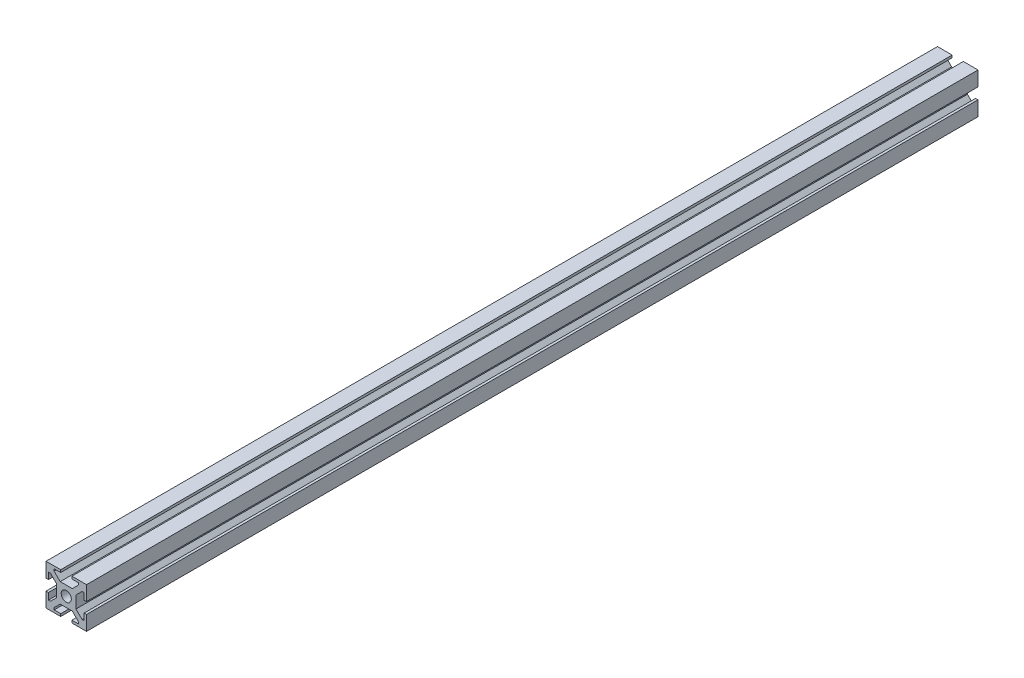
SolidWorks part; units mm, degrees
ref_plane "Plan de face" through (0, 0, 0) normal (0, 0, 1) x (1, 0, 0)
ref_plane "Plan de dessus" through (0, 0, 0) normal (0, 1, 0) x (1, 0, 0)
ref_plane "Plan de droite" through (0, 0, 0) normal (1, 0, 0) x (0, 0, -1)
sketch "Esquisse1" plane through (0, 0, 0) normal (0, 0, 1) x (1, 0, 0)
  line L1 (-22.5051, 0.0904) -> (-2.5051, 0.0904)
  line L2 (-22.5051, 0.0904) -> (-22.5051, -19.9096)
  line L3 (-22.5051, -19.9096) -> (-2.5051, -19.9096)
  line L4 (-2.5051, 0.0904) -> (-2.5051, -19.9096)
  dimension "D1" = 20
  dimension "D2" = 20
extrude "Boss.-Extru.1" add sketch "Esquisse1" along normal blind 440
sketch "Esquisse2" plane through (0, 0, 440) normal (0, 0, 1) x (1, 0, 0)
  line L0 (-22.5051, 0.0904) -> (-22.5051, -19.9096) construction
  line L1 (-22.5051, -7.1596) -> (-21.3051, -7.1596)
  line L2 (-22.5051, -7.1596) -> (-22.5051, -12.6596)
  line L3 (-22.5051, -12.6596) -> (-21.3051, -12.6596)
  line L4 (-21.3051, -7.1596) -> (-21.3051, -12.6596)
  line L5 (-2.5051, 0.0904) -> (-22.5051, 0.0904) construction
  line L6 (-15.2551, 0.0904) -> (-9.7551, 0.0904)
  line L7 (-15.2551, 0.0904) -> (-15.2551, -1.1096)
  line L8 (-15.2551, -1.1096) -> (-9.7551, -1.1096)
  line L9 (-9.7551, 0.0904) -> (-9.7551, -1.1096)
  line L10 (-2.5051, -19.9096) -> (-2.5051, 0.0904) construction
  line L11 (-2.5051, -7.1596) -> (-3.7051, -7.1596)
  line L12 (-2.5051, -7.1596) -> (-2.5051, -12.6596)
  line L13 (-2.5051, -12.6596) -> (-3.7051, -12.6596)
  line L14 (-3.7051, -7.1596) -> (-3.7051, -12.6596)
  line L15 (-22.5051, -19.9096) -> (-2.5051, -19.9096) construction
  line L16 (-15.2551, -19.9096) -> (-9.7551, -19.9096)
  line L17 (-15.2551, -19.9096) -> (-15.2551, -18.7096)
  line L18 (-15.2551, -18.7096) -> (-9.7551, -18.7096)
  line L19 (-9.7551, -19.9096) -> (-9.7551, -18.7096)
  dimension "D1" = 1.2
  dimension "D2" = 1.2
  dimension "D3" = 1.2
  dimension "D4" = 1.2
  dimension "D5" = 5.5
  dimension "D6" = 5.5
  dimension "D7" = 5.5
  dimension "D8" = 5.5
  dimension "D9" = 7.25
  dimension "D10" = 7.25
  dimension "D11" = 7.25
  dimension "D12" = 7.25
extrude "Enlèv. mat.-Extru.1" cut sketch "Esquisse2" against normal through all
sketch "Esquisse3" plane through (0, 0, 440) normal (0, 0, 1) x (1, 0, 0)
  line L0 (-15.2551, 0.0904) -> (-22.5051, 0.0904) construction
  line L1 (-21.3051, -15.9096) -> (-20.3051, -15.9096)
  line L2 (-21.3051, -15.9096) -> (-21.3051, -3.9096)
  line L3 (-21.3051, -3.9096) -> (-20.3051, -3.9096)
  line L4 (-17.3051, -12.9096) -> (-17.3051, -6.9096)
  line L5 (-18.5051, -1.1096) -> (-6.5051, -1.1096)
  line L6 (-18.5051, -1.1096) -> (-18.5051, -2.1096)
  line L7 (-15.5051, -5.1096) -> (-9.5051, -5.1096)
  line L8 (-6.5051, -1.1096) -> (-6.5051, -2.1096)
  line L9 (-3.7051, -3.9096) -> (-4.7051, -3.9096)
  line L10 (-3.7051, -3.9096) -> (-3.7051, -15.9096)
  line L11 (-3.7051, -15.9096) -> (-4.7051, -15.9096)
  line L12 (-7.7051, -6.9096) -> (-7.7051, -12.9096)
  line L13 (-6.5051, -18.7096) -> (-18.5051, -18.7096)
  line L14 (-6.5051, -18.7096) -> (-6.5051, -17.7096)
  line L15 (-9.5051, -14.7096) -> (-15.5051, -14.7096)
  line L16 (-18.5051, -18.7096) -> (-18.5051, -17.7096)
  line L17 (-2.5051, -7.1596) -> (-2.5051, 0.0904) construction
  line L18 (-15.2551, -1.1096) -> (-9.7551, -1.1096) construction
  line L19 (-3.7051, -7.1596) -> (-3.7051, -12.6596) construction
  line L20 (-9.7551, -19.9096) -> (-2.5051, -19.9096) construction
  line L21 (-22.5051, -12.6596) -> (-22.5051, -19.9096) construction
  line L22 (-22.5051, -19.9096) -> (-15.2551, -19.9096) construction
  line L23 (-15.5051, -14.7096) -> (-18.5051, -17.7096)
  line L24 (-20.3051, -15.9096) -> (-17.3051, -12.9096)
  line L25 (-6.5051, -17.7096) -> (-9.5051, -14.7096)
  line L26 (-4.7051, -15.9096) -> (-7.7051, -12.9096)
  line L27 (-4.7051, -3.9096) -> (-7.7051, -6.9096)
  line L28 (-9.5051, -5.1096) -> (-6.5051, -2.1096)
  line L29 (-18.5051, -2.1096) -> (-15.5051, -5.1096)
  line L30 (-20.3051, -3.9096) -> (-17.3051, -6.9096)
  point P1 (-17.3051, -3.9096)
  point P3 (-17.3051, -15.9096)
  point P5 (-6.5051, -5.1096)
  point P6 (-18.5051, -5.1096)
  point P9 (-7.7051, -15.9096)
  point P11 (-7.7051, -3.9096)
  point P13 (-18.5051, -14.7096)
  point P14 (-6.5051, -14.7096)
  point P24 (-6.1301, -19.9096)
  dimension "D1" = 4
  dimension "D2" = 4
  dimension "D3" = 4
  dimension "D4" = 4
  dimension "D5" = 12
  dimension "D6" = 4
  dimension "D7" = 12
  dimension "D8" = 4
  dimension "D9" = 0
  dimension "D10" = 0
  dimension "D11" = 4
  dimension "D12" = 12
  dimension "D13" = 12
  dimension "D14" = 4
  dimension "D15" = 1.2
  dimension "D16" = 1.2
  dimension "D17" = 3
  dimension "D18" = 3
  dimension "D19" = 3
  dimension "D20" = 3
  dimension "D21" = 3
  dimension "D22" = 3
  dimension "D23" = 3
  dimension "D24" = 3
  dimension "D25" = 3
  dimension "D26" = 3
  dimension "D27" = 3
  dimension "D28" = 3
  dimension "D29" = 3
  dimension "D30" = 3
  dimension "D31" = 3
  dimension "D32" = 3
extrude "Enlèv. mat.-Extru.2" cut sketch "Esquisse3" against normal through all
sketch "Esquisse4" plane through (0, 0, 440) normal (0, 0, 1) x (1, 0, 0)
  line L0 (-15.5051, -5.1096) -> (-9.5051, -5.1096) construction
  line L2 (-17.3051, -12.9096) -> (-17.3051, -6.9096) construction
  circle A0 centre (-12.5051, -9.9096) radius 2.5
  dimension "D1" = 5
  dimension "D2" = 4.8
  dimension "D3" = 4.8
extrude "Enlèv. mat.-Extru.3" cut sketch "Esquisse4" against normal through all
